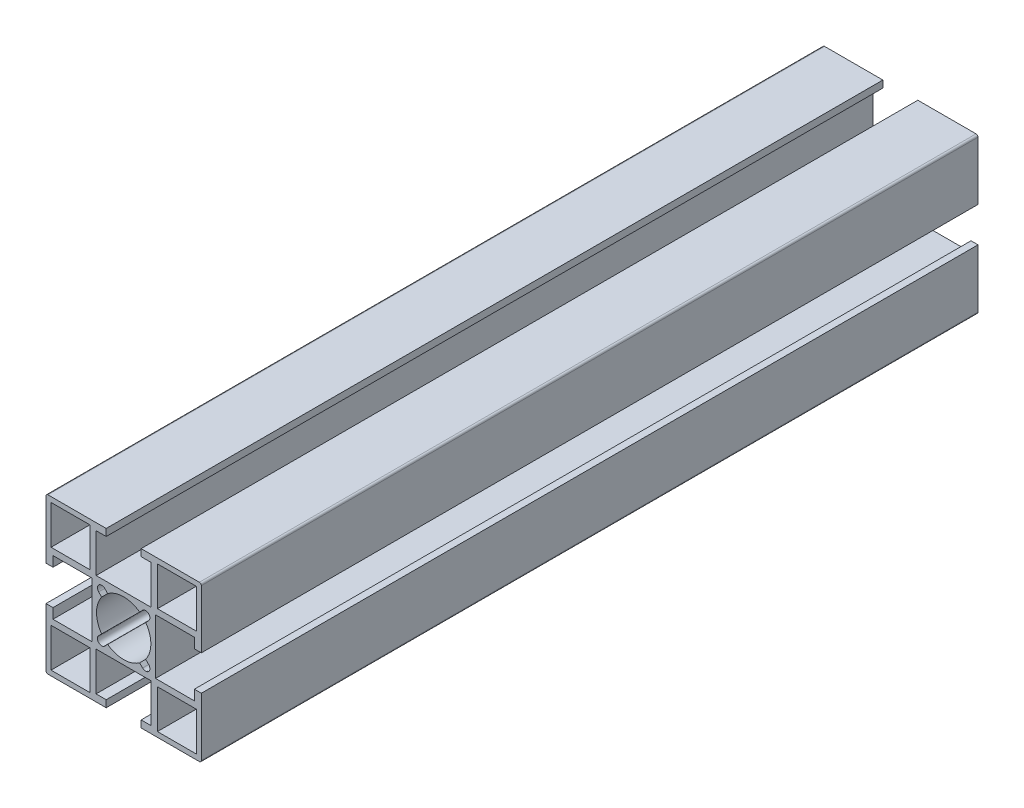
SolidWorks part; units mm, degrees
ref_plane "前视基准面" through (0, 0, 0) normal (0, 0, 1) x (1, 0, 0)
ref_plane "上视基准面" through (0, 0, 0) normal (0, 1, 0) x (1, 0, 0)
ref_plane "右视基准面" through (0, 0, 0) normal (1, 0, 0) x (0, 0, -1)
other "Configuration Table"
sketch "草图1" plane through (0, 0, 0) normal (1, 0, 0) x (0, 0, -1)
  line L0 (0, 0) -> (200, 0)
  dimension "D1" = 200
other "铝型材 40 X 40A X R0.5(1)"
ref_plane "基准面1" through (0, 0, 0) normal (0, 0, -1) x (0, 1, 0)
sketch "Sketch1" plane through (0, 0, 0) normal (0, 0, -1) x (0, 1, 0)
  line L0 (0, 0) -> (0, 16.3773) construction
  line L1 (0, 0) -> (-5.6569, 5.6569) construction
  line L2 (-19.5, 20) -> (-4.5, 20)
  line L3 (-20, 19.5) -> (-20, 4.5)
  line L4 (-19.5, -20) -> (-4.5, -20)
  line L5 (20, 19.5) -> (20, 4.5)
  line L6 (-4.879, 6.4347) -> (-4.1104, 5.6661)
  line L7 (-6.4347, 4.879) -> (-5.6661, 4.1104)
  line L8 (6.4347, 4.879) -> (5.6661, 4.1104)
  line L9 (0, 0) -> (20, 0) construction
  line L10 (4.879, 6.4347) -> (4.1104, 5.6661)
  line L11 (4.879, -6.4347) -> (4.1104, -5.6661)
  line L12 (6.4347, -4.879) -> (5.6661, -4.1104)
  line L13 (-6.4347, -4.879) -> (-5.6661, -4.1104)
  line L14 (-4.879, -6.4347) -> (-4.1104, -5.6661)
  line L15 (-4.5, 20) -> (-4.5, 18.2)
  line L16 (-18.7, 18.7) -> (-8.7, 18.7)
  line L17 (-18.7, 18.7) -> (-18.7, 8.7)
  line L18 (-18.7, 8.7) -> (-8.7, 8.7)
  line L19 (-8.7, 18.7) -> (-8.7, 8.7)
  line L20 (-7.1, 18.2) -> (-4.5, 18.2)
  line L21 (-7.1, 18.2) -> (-7.1, 8.2)
  line L22 (-7.1, 8.2) -> (7.1, 8.2)
  line L23 (7.1, 18.2) -> (7.1, 8.2)
  line L24 (4.5, 20) -> (4.5, 18.2)
  line L25 (4.5, 20) -> (19.5, 20)
  line L26 (4.5, 18.2) -> (7.1, 18.2)
  line L27 (8.7, 18.7) -> (8.7, 8.7)
  line L28 (18.7, 8.7) -> (8.7, 8.7)
  line L29 (18.7, 18.7) -> (18.7, 8.7)
  line L30 (18.7, 18.7) -> (8.7, 18.7)
  line L31 (18.2, 7.1) -> (8.2, 7.1)
  line L32 (18.2, 7.1) -> (18.2, 4.5)
  line L33 (20, 4.5) -> (18.2, 4.5)
  line L34 (8.2, 7.1) -> (8.2, -7.1)
  line L35 (18.2, -7.1) -> (8.2, -7.1)
  line L36 (18.2, -4.5) -> (18.2, -7.1)
  line L37 (20, -4.5) -> (18.2, -4.5)
  line L38 (7.1, -18.2) -> (7.1, -8.2)
  line L39 (7.1, -18.2) -> (4.5, -18.2)
  line L40 (4.5, -20) -> (4.5, -18.2)
  line L41 (7.1, -8.2) -> (-7.1, -8.2)
  line L42 (-7.1, -18.2) -> (-7.1, -8.2)
  line L43 (-4.5, -18.2) -> (-7.1, -18.2)
  line L44 (-4.5, -20) -> (-4.5, -18.2)
  line L45 (-18.2, -7.1) -> (-8.2, -7.1)
  line L46 (-18.2, -7.1) -> (-18.2, -4.5)
  line L47 (-20, -4.5) -> (-18.2, -4.5)
  line L48 (-8.2, -7.1) -> (-8.2, 7.1)
  line L49 (-18.2, 7.1) -> (-8.2, 7.1)
  line L50 (-18.2, 4.5) -> (-18.2, 7.1)
  line L51 (-20, 4.5) -> (-18.2, 4.5)
  line L52 (4.5, -20) -> (19.5, -20)
  line L53 (-20, -4.5) -> (-20, -19.5)
  line L54 (20, -4.5) -> (20, -19.5)
  line L55 (18.7, -18.7) -> (18.7, -8.7)
  line L56 (18.7, -8.7) -> (8.7, -8.7)
  line L57 (8.7, -18.7) -> (8.7, -8.7)
  line L58 (18.7, -18.7) -> (8.7, -18.7)
  line L59 (-8.7, -18.7) -> (-8.7, -8.7)
  line L60 (-18.7, -8.7) -> (-8.7, -8.7)
  line L61 (-18.7, -18.7) -> (-8.7, -18.7)
  line L62 (-18.7, -18.7) -> (-18.7, -8.7)
  arc A0 (-4.1104, 5.6661) -> (4.1104, 5.6661) centre (0, 0) cw
  arc A1 (-4.879, 6.4347) -> (-6.4347, 4.879) centre (-5.6569, 5.6569) ccw
  arc A2 (-4.1104, -5.6661) -> (4.1104, -5.6661) centre (0, 0) ccw
  arc A3 (-5.6661, 4.1104) -> (-5.6661, -4.1104) centre (0, 0) ccw
  arc A4 (6.4347, 4.879) -> (4.879, 6.4347) centre (5.6569, 5.6569) ccw
  arc A5 (4.879, -6.4347) -> (6.4347, -4.879) centre (5.6569, -5.6569) ccw
  arc A6 (-6.4347, -4.879) -> (-4.879, -6.4347) centre (-5.6569, -5.6569) ccw
  arc A7 (5.6661, 4.1104) -> (5.6661, -4.1104) centre (0, 0) cw
  arc A8 (-19.5, 20) -> (-20, 19.5) centre (-19.5, 19.5) ccw
  arc A9 (19.5, 20) -> (20, 19.5) centre (19.5, 19.5) cw
  arc A10 (19.5, -20) -> (20, -19.5) centre (19.5, -19.5) ccw
  arc A11 (-20, -19.5) -> (-19.5, -20) centre (-19.5, -19.5) ccw
  point P86 (20, 20)
  point P87 (-20, 20)
  point P88 (-20, -20)
  point P89 (20, -20)
  point P90 (0, 0)
  dimension "D2" = 7
  dimension "D3" = 45
  dimension "D4" = 1.1
  dimension "D5" = 1.8
  dimension "D6" = 8
  dimension "D7" = 1.3
  dimension "D8" = 14.2
  dimension "D10" = 10
  dimension "D11" = 10
  dimension "D12" = 40
  dimension "D13" = 9
  dimension "D14" = 0.5
  dimension "D9" = 1.3
